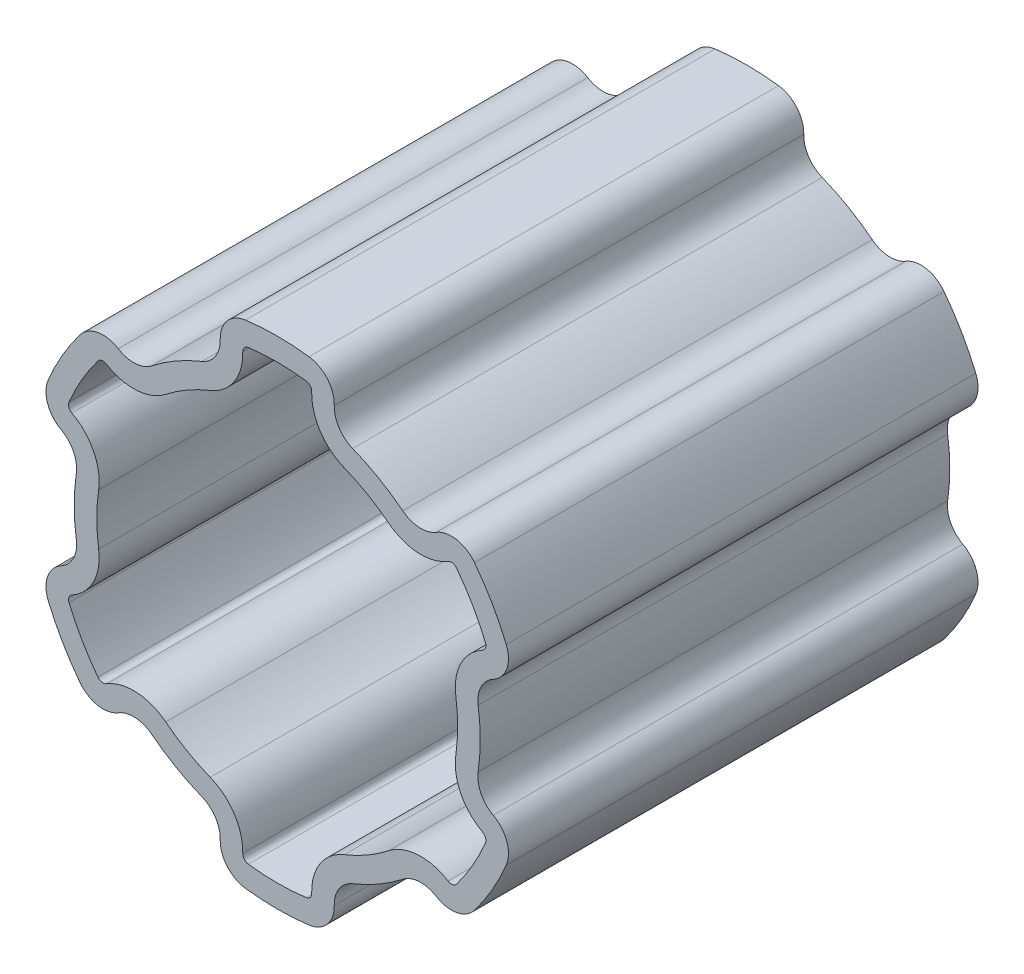
SolidWorks part; units mm, degrees
material "6061 Alloy"
ref_plane "Front Plane" through (0, 0, 0) normal (0, 0, 1) x (1, 0, 0)
ref_plane "Top Plane" through (0, 0, 0) normal (0, 1, 0) x (1, 0, 0)
ref_plane "Right Plane" through (0, 0, 0) normal (1, 0, 0) x (0, 0, -1)
sketch "Sketch1" plane through (0, 0, 0) normal (0, 0, 1) x (1, 0, 0)
  arc A0 (-4.7152, 11.7788) -> (-7.8431, 9.9729) centre (0, 0) ccw
  arc A1 (-12.0149, 9.7349) -> (-7.8431, 9.9729) centre (-10.0994, 12.842) ccw
  arc A2 (-12.0149, 9.7349) -> (-12.6087, 9.6249) centre (-12.251, 9.3519) ccw
  arc A3 (-12.6087, 9.6249) -> (-14.6398, 6.107) centre (0, 0) ccw
  arc A4 (-14.6398, 6.107) -> (-14.4381, 5.5377) centre (-14.2245, 5.9338) ccw
  arc A5 (-12.5583, 1.8059) -> (-14.4381, 5.5377) centre (-16.1712, 2.3254) ccw
  arc A6 (-12.5583, 1.8059) -> (-12.6875, 0) centre (0, 0) ccw
  arc A7 (-12.6875, 0) -> (-12.5583, -1.8059) centre (0, 0) ccw
  arc A8 (-14.4381, -5.5377) -> (-12.5583, -1.8059) centre (-16.1712, -2.3254) ccw
  arc A9 (-14.4381, -5.5377) -> (-14.6398, -6.107) centre (-14.2245, -5.9338) ccw
  arc A10 (-14.6398, -6.107) -> (-12.6087, -9.6249) centre (0, 0) ccw
  arc A11 (-12.6087, -9.6249) -> (-12.0149, -9.7349) centre (-12.251, -9.3519) ccw
  arc A12 (-7.8431, -9.9729) -> (-12.0149, -9.7349) centre (-10.0994, -12.842) ccw
  arc A13 (-7.8431, -9.9729) -> (-4.7152, -11.7788) centre (0, 0) ccw
  arc A14 (-2.4233, -15.2726) -> (-4.7152, -11.7788) centre (-6.0718, -15.1673) ccw
  arc A15 (-2.4233, -15.2726) -> (-2.0311, -15.7319) centre (-1.9735, -15.2856) ccw
  arc A16 (-2.0311, -15.7319) -> (2.0311, -15.7319) centre (0, 0) ccw
  arc A17 (2.0311, -15.7319) -> (2.4235, -15.2856) centre (1.9735, -15.2856) ccw
  arc A18 (2.4235, -15.2856) -> (2.4233, -15.2726) centre (1.9735, -15.2856) ccw
  arc A19 (2.4217, -15.1673) -> (2.4233, -15.2726) centre (6.0718, -15.1673) ccw
  arc A20 (4.7152, -11.7788) -> (2.4217, -15.1673) centre (6.0718, -15.1673) ccw
  arc A21 (4.7152, -11.7788) -> (7.8431, -9.9729) centre (0, 0) ccw
  arc A22 (12.0149, -9.7349) -> (7.8431, -9.9729) centre (10.0994, -12.842) ccw
  arc A23 (12.0149, -9.7349) -> (12.6087, -9.6249) centre (12.251, -9.3519) ccw
  arc A24 (12.6087, -9.6249) -> (14.6398, -6.107) centre (0, 0) ccw
  arc A25 (14.6398, -6.107) -> (14.6745, -5.9338) centre (14.2245, -5.9338) ccw
  arc A26 (14.6745, -5.9338) -> (14.4381, -5.5377) centre (14.2245, -5.9338) ccw
  arc A27 (12.5212, -2.3254) -> (14.4381, -5.5377) centre (16.1712, -2.3254) ccw
  arc A28 (12.5583, -1.8059) -> (12.5212, -2.3254) centre (16.1712, -2.3254) ccw
  arc A29 (12.5583, -1.8059) -> (12.5583, 1.8059) centre (0, 0) ccw
  arc A30 (12.5212, 2.3254) -> (12.5583, 1.8059) centre (16.1712, 2.3254) ccw
  arc A31 (14.4381, 5.5377) -> (12.5212, 2.3254) centre (16.1712, 2.3254) ccw
  arc A32 (14.4381, 5.5377) -> (14.6745, 5.9338) centre (14.2245, 5.9338) ccw
  arc A33 (14.6745, 5.9338) -> (14.6398, 6.107) centre (14.2245, 5.9338) ccw
  arc A34 (14.6398, 6.107) -> (12.6087, 9.6249) centre (0, 0) ccw
  arc A35 (12.6087, 9.6249) -> (12.0149, 9.7349) centre (12.251, 9.3519) ccw
  arc A36 (7.8431, 9.9729) -> (12.0149, 9.7349) centre (10.0994, 12.842) ccw
  arc A37 (7.8431, 9.9729) -> (4.7152, 11.7788) centre (0, 0) ccw
  arc A38 (2.4217, 15.1673) -> (4.7152, 11.7788) centre (6.0718, 15.1673) ccw
  arc A39 (2.4233, 15.2726) -> (2.4217, 15.1673) centre (6.0718, 15.1673) ccw
  arc A40 (2.4233, 15.2726) -> (2.4235, 15.2856) centre (1.9735, 15.2856) ccw
  arc A41 (2.4235, 15.2856) -> (2.0311, 15.7319) centre (1.9735, 15.2856) ccw
  arc A42 (2.0311, 15.7319) -> (-2.0311, 15.7319) centre (0, 0) ccw
  arc A43 (-2.0311, 15.7319) -> (-2.4233, 15.2726) centre (-1.9735, 15.2856) ccw
  arc A44 (-4.7152, 11.7788) -> (-2.4233, 15.2726) centre (-6.0718, 15.1673) ccw
  arc A45 (-5.3052, 13.2526) -> (-8.8244, 11.2207) centre (0, 0) ccw
  arc A46 (-11.1818, 11.0863) -> (-8.8244, 11.2207) centre (-10.0994, 12.842) ccw
  arc A47 (-11.1818, 11.0863) -> (-13.8706, 10.5882) centre (-12.251, 9.3519) ccw
  arc A48 (-13.8706, 10.5882) -> (-16.1049, 6.7182) centre (0, 0) ccw
  arc A49 (-16.1049, 6.7182) -> (-15.1919, 4.1406) centre (-14.2245, 5.9338) ccw
  arc A50 (-14.1297, 2.0318) -> (-15.1919, 4.1406) centre (-16.1712, 2.3254) ccw
  arc A51 (-14.1297, 2.0318) -> (-14.275, 0) centre (0, 0) ccw
  arc A52 (-14.275, 0) -> (-14.1297, -2.0318) centre (0, 0) ccw
  arc A53 (-15.1919, -4.1406) -> (-14.1297, -2.0318) centre (-16.1712, -2.3254) ccw
  arc A54 (-15.1919, -4.1406) -> (-16.1049, -6.7182) centre (-14.2245, -5.9338) ccw
  arc A55 (-16.1049, -6.7182) -> (-13.8706, -10.5882) centre (0, 0) ccw
  arc A56 (-13.8706, -10.5882) -> (-11.1818, -11.0863) centre (-12.251, -9.3519) ccw
  arc A57 (-8.8244, -11.2207) -> (-11.1818, -11.0863) centre (-10.0994, -12.842) ccw
  arc A58 (-8.8244, -11.2207) -> (-5.3052, -13.2526) centre (0, 0) ccw
  arc A59 (-4.0101, -15.2268) -> (-5.3052, -13.2526) centre (-6.0718, -15.1673) ccw
  arc A60 (-4.0101, -15.2268) -> (-2.2343, -17.3064) centre (-1.9735, -15.2856) ccw
  arc A61 (-2.2343, -17.3064) -> (2.2343, -17.3064) centre (0, 0) ccw
  arc A62 (2.2343, -17.3064) -> (4.011, -15.2856) centre (1.9735, -15.2856) ccw
  arc A63 (4.011, -15.2856) -> (4.0101, -15.2268) centre (1.9735, -15.2856) ccw
  arc A64 (4.0092, -15.1673) -> (4.0101, -15.2268) centre (6.0718, -15.1673) ccw
  arc A65 (5.3052, -13.2526) -> (4.0092, -15.1673) centre (6.0718, -15.1673) ccw
  arc A66 (5.3052, -13.2526) -> (8.8244, -11.2207) centre (0, 0) ccw
  arc A67 (11.1818, -11.0863) -> (8.8244, -11.2207) centre (10.0994, -12.842) ccw
  arc A68 (11.1818, -11.0863) -> (13.8706, -10.5882) centre (12.251, -9.3519) ccw
  arc A69 (13.8706, -10.5882) -> (16.1049, -6.7182) centre (0, 0) ccw
  arc A70 (16.1049, -6.7182) -> (16.262, -5.9338) centre (14.2245, -5.9338) ccw
  arc A71 (16.262, -5.9338) -> (15.1919, -4.1406) centre (14.2245, -5.9338) ccw
  arc A72 (14.1087, -2.3254) -> (15.1919, -4.1406) centre (16.1712, -2.3254) ccw
  arc A73 (14.1297, -2.0318) -> (14.1087, -2.3254) centre (16.1712, -2.3254) ccw
  arc A74 (14.1297, -2.0318) -> (14.1297, 2.0318) centre (0, 0) ccw
  arc A75 (14.1087, 2.3254) -> (14.1297, 2.0318) centre (16.1712, 2.3254) ccw
  arc A76 (15.1919, 4.1406) -> (14.1087, 2.3254) centre (16.1712, 2.3254) ccw
  arc A77 (15.1919, 4.1406) -> (16.262, 5.9338) centre (14.2245, 5.9338) ccw
  arc A78 (16.262, 5.9338) -> (16.1049, 6.7182) centre (14.2245, 5.9338) ccw
  arc A79 (16.1049, 6.7182) -> (13.8706, 10.5882) centre (0, 0) ccw
  arc A80 (13.8706, 10.5882) -> (11.1818, 11.0863) centre (12.251, 9.3519) ccw
  arc A81 (8.8244, 11.2207) -> (11.1818, 11.0863) centre (10.0994, 12.842) ccw
  arc A82 (8.8244, 11.2207) -> (5.3052, 13.2526) centre (0, 0) ccw
  arc A83 (4.0092, 15.1673) -> (5.3052, 13.2526) centre (6.0718, 15.1673) ccw
  arc A84 (4.0101, 15.2268) -> (4.0092, 15.1673) centre (6.0718, 15.1673) ccw
  arc A85 (4.0101, 15.2268) -> (4.011, 15.2856) centre (1.9735, 15.2856) ccw
  arc A86 (4.011, 15.2856) -> (2.2343, 17.3064) centre (1.9735, 15.2856) ccw
  arc A87 (2.2343, 17.3064) -> (-2.2343, 17.3064) centre (0, 0) ccw
  arc A88 (-2.2343, 17.3064) -> (-4.0101, 15.2268) centre (-1.9735, 15.2856) ccw
  arc A89 (-5.3052, 13.2526) -> (-4.0101, 15.2268) centre (-6.0718, 15.1673) ccw
extrude "Boss-Extrude1" add sketch "Sketch1" along normal blind 33.02
equation "\"Length\" = 1.3"
equation "\"D1@Boss-Extrude1\"=\"Length\""
